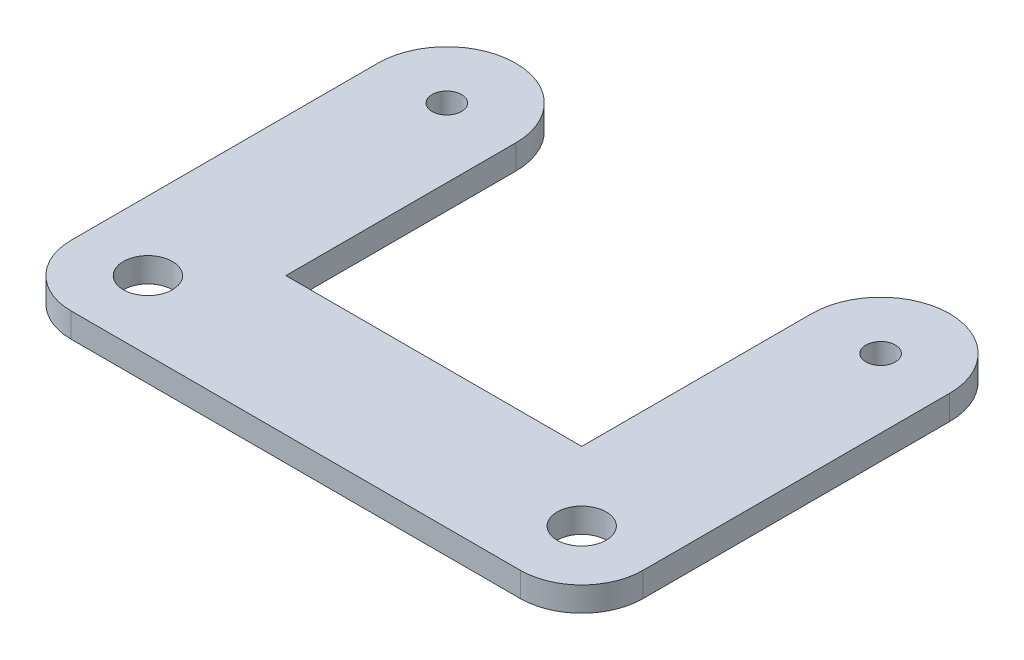
SolidWorks part; units mm, degrees
ref_plane "Front Plane" through (0, 0, 0) normal (0, 0, 1) x (1, 0, 0)
ref_plane "Top Plane" through (0, 0, 0) normal (0, 1, 0) x (1, 0, 0)
ref_plane "Right Plane" through (0, 0, 0) normal (1, 0, 0) x (0, 0, -1)
sketch "Sketch1" plane through (0, 0, 0) normal (0, 1, 0) x (1, 0, 0)
  line L0 (-32.975, 0) -> (-37.775, 0) construction
  line L1 (32.975, 0) -> (37.775, 0) construction
  line L2 (32.975, 0) -> (-32.975, 0) construction
  line L3 (-24.125, 0) -> (-24.125, -37.5)
  line L4 (-24.125, -37.5) -> (24.125, -37.5)
  line L5 (24.125, -37.5) -> (24.125, 0)
  line L6 (-46.625, 0) -> (-46.625, -60)
  line L7 (-46.625, -60) -> (46.625, -60)
  line L8 (46.625, -60) -> (46.625, 0)
  line L12 (-46.625, -60) -> (-24.125, -37.5) construction
  line L13 (24.125, -37.5) -> (46.625, -60) construction
  circle A0 centre (-35.375, 0) radius 2.4
  circle A2 centre (35.375, 0) radius 2.4
  circle A3 centre (-35.375, 0) radius 11.25
  circle A4 centre (35.375, 0) radius 11.25
  circle A5 centre (-35.375, -48.75) radius 4
  circle A6 centre (35.375, -48.75) radius 4
  dimension "D4" = 22.5
  dimension "D10" = 8
  dimension "D2" = 4.8
  dimension "D5" = 37.5
  dimension "D6" = 22.5
  dimension "D7" = 70.75
extrude "Boss-Extrude1" add sketch "Sketch1" along normal blind 4 contours A4 L5 L4 L3 A3 L6 L7 L8 A6 A5 | A3 A0 | A4 A2
fillet "Fillet1" radius 10 2 edges at (46.625, 2, 60) (-46.625, 2, 60)
equation "\"m3 hole\"= 3.2"
equation "\"m4 hole\"= 4.2"
equation "\"m5 hole\"= 5.2"
equation "\"m6 hole\"= 6.2"
equation "\"m8 hole\"= 8.2"
equation "\"m3 tapped\"= 2.5"
equation "\"m4 tapped\"= 3.3"
equation "\"m5 tapped\"= 4.2"
equation "\"m6 tapped\"= 5"
equation "\"m8 tapped\"= 6.8"
equation "\"e\"=10"
